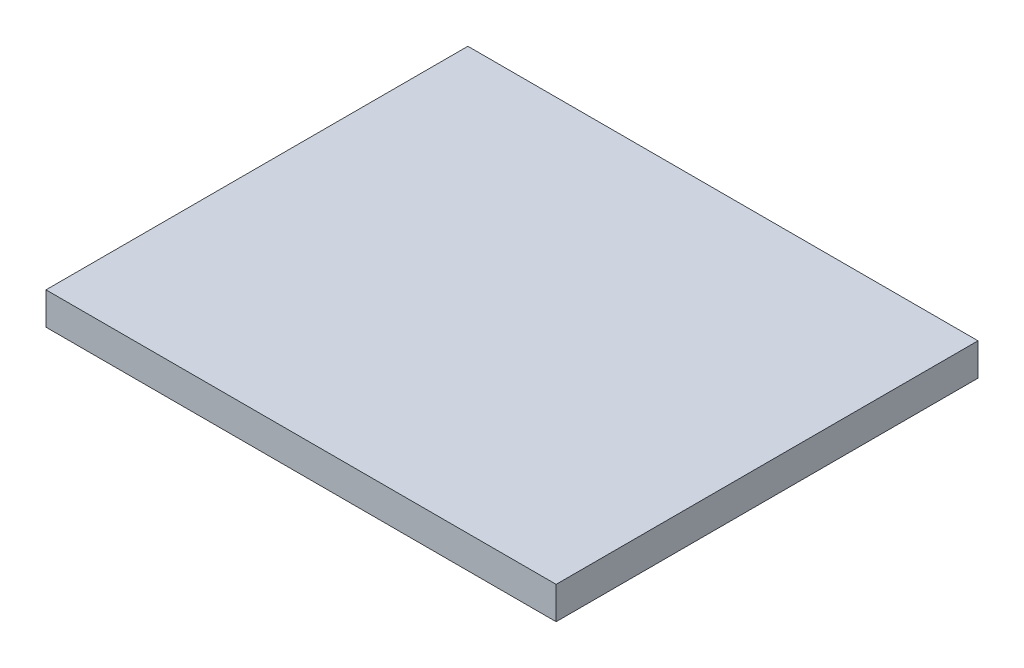
SolidWorks part; units mm, degrees
ref_plane "Front Plane" through (0, 0, 0) normal (0, 0, 1) x (1, 0, 0)
ref_plane "Top Plane" through (0, 0, 0) normal (0, 1, 0) x (1, 0, 0)
ref_plane "Right Plane" through (0, 0, 0) normal (1, 0, 0) x (0, 0, -1)
sketch "Sketch1" plane through (0, 0, 0) normal (0, 1, 0) x (1, 0, 0)
  line L1 (-25, -20.675) -> (25, -20.675)
  line L2 (-25, -20.675) -> (-25, 20.675)
  line L3 (-25, 20.675) -> (25, 20.675)
  line L4 (25, -20.675) -> (25, 20.675)
  line L5 (-25, -20.675) -> (25, 20.675) construction
  line L6 (-25, 20.675) -> (25, -20.675) construction
  point P0 (0, 0)
  dimension "D1" = 50
  dimension "D2" = 41.35
extrude "Boss-Extrude1" add sketch "Sketch1" along normal blind 3.175
